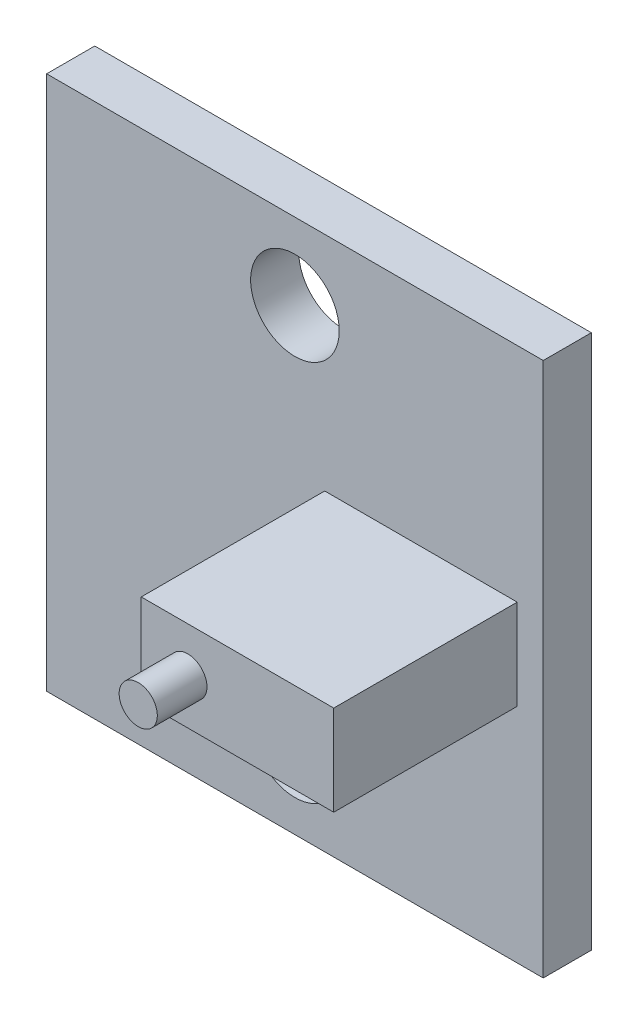
SolidWorks part; units mm, degrees
ref_plane "Front Plane" through (0, 0, 0) normal (0, 0, 1) x (1, 0, 0)
ref_plane "Top Plane" through (0, 0, 0) normal (0, 1, 0) x (1, 0, 0)
ref_plane "Right Plane" through (0, 0, 0) normal (1, 0, 0) x (0, 0, -1)
sketch "Sketch1" plane through (0, 0, 0) normal (0, 0, 1) x (1, 0, 0)
  line L1 (8.255, -8.89) -> (-8.255, -8.89)
  line L2 (8.255, -8.89) -> (8.255, 8.89)
  line L3 (8.255, 8.89) -> (-8.255, 8.89)
  line L4 (-8.255, -8.89) -> (-8.255, 8.89)
  line L5 (8.255, -8.89) -> (-8.255, 8.89) construction
  line L6 (8.255, 8.89) -> (-8.255, -8.89) construction
  point P0 (0, 0)
  dimension "D1" = 16.51
  dimension "D2" = 17.78
extrude "Boss-Extrude1" add sketch "Sketch1" along normal blind 1.6
sketch "Sketch2" plane through (0, 0, 1.6) normal (0, 0, 1) x (1, 0, 0)
  line L0 (0, 6.35) -> (0, -6.35) construction
  dimension "D1" = 12.7
hole_wizard "#4 Clearance Hole1" positions "3DSketch1" profile "Sketch3" hole size "#4" standard "ANSI Inch"
sketch3d "3DSketch1"
  point P0 (0, 6.35, 1.6)
  point P3 (0, -6.35, 1.6)
sketch "Sketch3" plane through (0, 6.35, 1.6) normal (1, 0, 0) x (0, -1, 0)
  line L0 (0, 0) -> (0, 7.2352)
  line L1 (0, 7.2352) -> (1.4732, 6.35)
  line L2 (1.4732, 6.35) -> (1.4732, 0)
  line L5 (1.4732, 0) -> (0, 0)
  line L10 (0, 7.2352) -> (-1.4732, 6.35) construction
  line L11 (0, -6.35) -> (0, 107.95) construction
  dimension "Hole Dia." = 2.9464
  dimension "Hole Depth" = 6.35
  dimension "Drill Angle" = 118
sketch "Sketch4" plane through (0, 0, 1.6) normal (0, 0, 1) x (1, 0, 0)
  line L1 (0.99, 1.5) -> (7.39, 1.5)
  line L2 (0.99, 1.5) -> (0.99, -1.5)
  line L3 (0.99, -1.5) -> (7.39, -1.5)
  line L4 (7.39, 1.5) -> (7.39, -1.5)
  line L5 (0.99, 1.5) -> (7.39, -1.5) construction
  line L6 (0.99, -1.5) -> (7.39, 1.5) construction
  point P0 (4.19, 0)
  point P5 (0, 0)
  dimension "D1" = 6.4
  dimension "D2" = 3
  dimension "D3" = 4.19
extrude "Boss-Extrude2" add sketch "Sketch4" along normal blind 6.1
sketch "Sketch5" plane through (0, 0, 7.7) normal (0, 0, 1) x (1, 0, 0)
  line L1 (7.39, 1.5) -> (0.99, 1.5) construction
  circle A0 centre (2.54, 0) radius 0.635
  point P2 (0, 0)
  point P3 (0, 0)
  point P5 (-0.4616, 0)
  point P8 (4.19, 1.5)
  dimension "D1" = 1.27
  dimension "D2" = 1.65
extrude "Boss-Extrude3" add sketch "Sketch5" along normal blind 1.65
